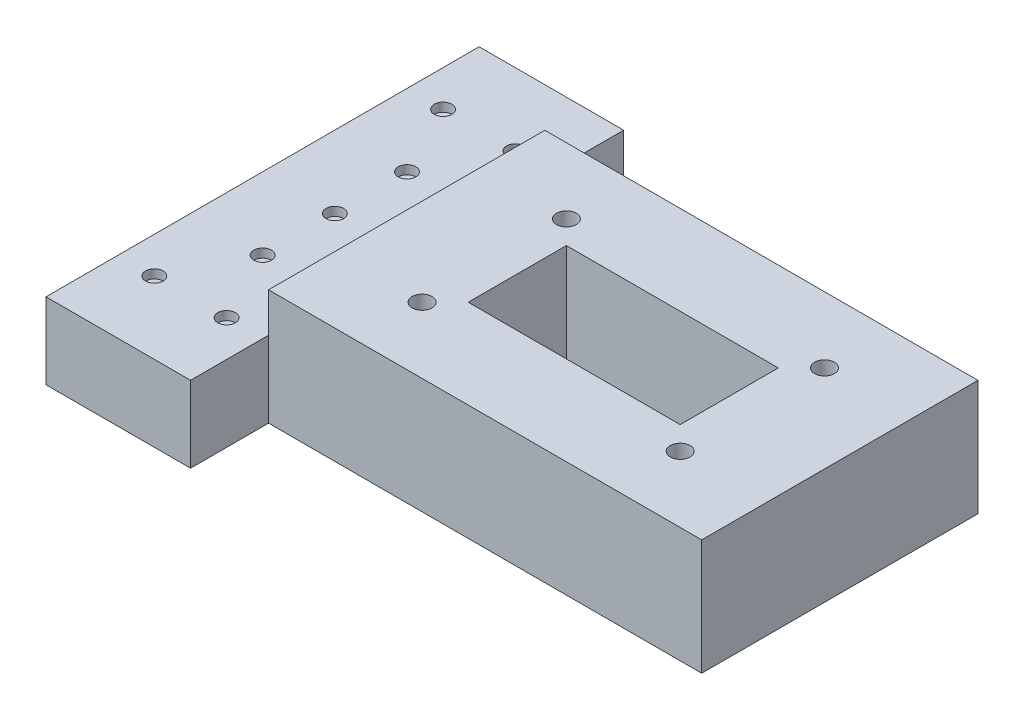
SolidWorks part; units mm, degrees
ref_plane "Front Plane" through (0, 0, 0) normal (0, 0, 1) x (1, 0, 0)
ref_plane "Top Plane" through (0, 0, 0) normal (0, 1, 0) x (1, 0, 0)
ref_plane "Right Plane" through (0, 0, 0) normal (1, 0, 0) x (0, 0, -1)
sketch "Sketch1" plane through (0, 0, 0) normal (0, 1, 0) x (1, 0, 0)
  line L0 (-111.76, 0) -> (-111.76, 9.42)
  line L1 (0, 0) -> (-111.76, 0)
  line L2 (0, 0) -> (0, 75.69)
  line L3 (0, 75.69) -> (-111.76, 75.69)
  line L4 (-111.76, 0) -> (-111.76, 9.42)
  line L5 (-111.76, 9.42) -> (-100.58, 9.42)
  line L7 (-111.76, 16.28) -> (-100.58, 16.28)
  line L8 (-111.76, 16.28) -> (-111.76, 75.69)
  line L9 (0, 0) -> (0, 37.845)
  line L10 (0, 37.845) -> (-111.76, 37.845)
  line L11 (-55.88, 75.69) -> (-55.88, 0)
  line L12 (-111.76, 66.27) -> (-100.58, 66.27)
  line L13 (-111.76, 59.41) -> (-100.58, 59.41)
  line L14 (0, 9.42) -> (-11.18, 9.42)
  line L15 (0, 16.28) -> (-11.18, 16.28)
  line L16 (0, 59.41) -> (-11.18, 59.41)
  line L17 (0, 66.27) -> (-11.18, 66.27)
  arc A0 (-100.58, 9.42) -> (-100.58, 16.28) centre (-100.58, 12.85) ccw
  arc A1 (-100.58, 66.27) -> (-100.58, 59.41) centre (-100.58, 62.84) cw
  arc A2 (-11.18, 9.42) -> (-11.18, 16.28) centre (-11.18, 12.85) cw
  arc A3 (-11.18, 66.27) -> (-11.18, 59.41) centre (-11.18, 62.84) ccw
  dimension "D1" = 111.76
  dimension "D2" = 75.69
sketch "Sketch2" plane through (0, 0, 0) normal (0, 1, 0) x (1, 0, 0)
  line L0 (-55.88, 0) -> (-55.88, 75.69)
  line L1 (-111.76, 0) -> (-121.76, 0)
  line L2 (-111.76, 0) -> (-111.76, -10)
  line L3 (-111.76, -10) -> (-121.76, -10)
  line L4 (-121.76, 0) -> (-121.76, -10)
  line L5 (0, 75.69) -> (10, 75.69)
  line L6 (0, 75.69) -> (0, 85.69)
  line L7 (0, 85.69) -> (10, 85.69)
  line L8 (10, 75.69) -> (10, 85.69)
  line L9 (-111.76, 37.845) -> (0, 37.845)
  circle A0 centre (-100.58, 12.85) radius 3.43
  circle A1 centre (-100.58, 12.85) radius 8
  circle A2 centre (-100.58, 62.84) radius 8
  circle A3 centre (-11.18, 12.85) radius 8
  circle A4 centre (-11.18, 62.84) radius 8
  dimension "D1" = 10
  dimension "D2" = 10
  dimension "D3" = 10
  dimension "D4" = 10
sketch "Sketch3" plane through (0, 0, 0) normal (0, 1, 0) x (1, 0, 0)
  line L0 (-100.58, 54.84) -> (-92.58, 54.84)
  line L1 (-121.76, -10) -> (-108.58, -10)
  line L2 (-121.76, -10) -> (-121.76, 12.85)
  line L5 (-108.58, -10) -> (-11.18, -10)
  line L9 (10, 85.69) -> (-3.18, 85.69)
  line L10 (10, 85.69) -> (10, 62.84)
  line L14 (10, 62.84) -> (10, -10)
  line L15 (10, -10) -> (-3.18, -10)
  line L19 (-11.18, -10) -> (-3.18, -10)
  line L22 (-121.76, 12.85) -> (-121.76, 62.84)
  line L26 (-121.76, 62.84) -> (-121.76, 85.69)
  line L27 (-121.76, 85.69) -> (-108.58, 85.69)
  line L29 (-108.58, 85.69) -> (-11.18, 85.69)
  line L35 (-11.18, 85.69) -> (-3.18, 85.69)
  line L37 (-92.58, 62.84) -> (-92.58, 54.84)
  line L38 (-19.18, 12.85) -> (-19.18, 20.85)
  line L39 (-11.18, 20.85) -> (-19.18, 20.85)
  line L41 (-92.58, 54.84) -> (-19.18, 54.84)
  line L42 (-92.58, 54.84) -> (-92.58, 20.85)
  line L43 (-92.58, 20.85) -> (-19.18, 20.85)
  line L44 (-19.18, 54.84) -> (-19.18, 20.85)
  circle A1 centre (-11.18, 12.85) radius 8 construction
  circle A3 centre (-100.58, 62.84) radius 8 construction
  circle A8 centre (-100.58, 62.84) radius 3.43
  circle A9 centre (-11.18, 62.84) radius 3.43
  circle A10 centre (-11.18, 12.85) radius 3.43
  circle A11 centre (-100.58, 12.85) radius 3.43
sketch "Sketch4" plane through (0, 0, 0) normal (0, 1, 0) x (1, 0, 0)
  line L0 (-108.58, 62.84) -> (-108.58, 70.84)
  line L1 (-108.58, 12.85) -> (-108.58, 4.85)
  line L2 (-108.58, 70.84) -> (-121.76, 70.84)
  line L3 (-108.58, 70.84) -> (-108.58, 85.69)
  line L4 (-108.58, 85.69) -> (-121.76, 85.69)
  line L5 (-121.76, 70.84) -> (-121.76, 85.69)
  line L6 (-55.88, 0) -> (-55.88, 75.69)
  line L7 (-108.58, 4.85) -> (-121.76, 4.85)
  line L8 (-108.58, 4.85) -> (-108.58, -10)
  line L9 (-108.58, -10) -> (-121.76, -10)
  line L10 (-121.76, 4.85) -> (-121.76, -10)
  line L11 (0, 0) -> (-111.76, 0) construction
  line L12 (10, 4.85) -> (10, -10)
  line L13 (-3.18, -10) -> (10, -10)
  line L14 (-3.18, 4.85) -> (-3.18, -10)
  line L15 (-3.18, 4.85) -> (10, 4.85)
  line L16 (-3.18, 70.84) -> (10, 70.84)
  line L17 (10, 70.84) -> (10, 85.69)
  line L18 (-3.18, 85.69) -> (10, 85.69)
  line L19 (-3.18, 70.84) -> (-3.18, 85.69)
  circle A0 centre (-100.58, 62.84) radius 8 construction
  circle A1 centre (-100.58, 12.85) radius 8 construction
sketch "Sketch8" plane through (0, 0, 0) normal (0, 1, 0) x (1, 0, 0)
  line L1 (-92.58, 20.85) -> (-19.18, 20.85)
  line L2 (-92.58, 20.85) -> (-92.58, 54.84)
  line L3 (-92.58, 54.84) -> (-19.18, 54.84)
  line L4 (-19.18, 20.85) -> (-19.18, 54.84)
  line L5 (-121.76, 85.69) -> (10, 85.69)
  line L6 (-121.76, 85.69) -> (-121.76, -10)
  line L7 (-121.76, -10) -> (10, -10)
  line L8 (10, 85.69) -> (10, -10)
  circle A0 centre (-100.58, 12.85) radius 3.43
  circle A1 centre (-100.58, 62.84) radius 3.43
  circle A2 centre (-11.18, 62.84) radius 3.43
  circle A3 centre (-11.18, 12.85) radius 3.43
extrude "Boss-Extrude4" add sketch "Sketch8" along normal blind 40
sketch "Sketch9" plane through (0, 0, 0) normal (0, -1, 0) x (1, 0, 0)
  circle A0 centre (-100.58, -12.85) radius 8
  circle A1 centre (-11.18, -12.85) radius 8
  circle A2 centre (-11.18, -62.84) radius 8
  circle A3 centre (-100.58, -62.84) radius 8
extrude "Cut-Extrude2" cut sketch "Sketch9" against normal blind 8
sketch "Sketch10" plane through (0, 0, 0) normal (0, -1, 0) x (1, 0, 0)
  line L1 (-121.76, 10) -> (10, 10)
  line L2 (-121.76, 10) -> (-121.76, 60)
  line L3 (-121.76, 60) -> (10, 60)
  line L4 (10, 10) -> (10, 60)
  line L5 (-121.76, 60) -> (-108.58, 60)
  line L6 (-121.76, 60) -> (-121.76, 45.15)
  line L7 (-121.76, 45.15) -> (-108.58, 45.15)
  line L8 (-108.58, 60) -> (-108.58, 45.15)
  dimension "D1" = 50
  dimension "D2" = 13.18
  dimension "D3" = 14.85
sketch "Sketch11" plane through (0, 40, 0) normal (0, 1, 0) x (1, 0, 0)
  line L1 (-121.76, -60) -> (10, -60)
  line L2 (-121.76, -60) -> (-121.76, -10)
  line L3 (-121.76, -10) -> (10, -10)
  line L4 (10, -60) -> (10, -10)
sketch "Sketch12" plane through (0, 0, 0) normal (0, -1, 0) x (1, 0, 0)
  line L1 (-121.76, 10) -> (-130.88, 10)
  line L2 (-130.88, 10) -> (19.12, 10)
  line L3 (19.12, 10) -> (19.12, -85.69)
  line L4 (19.12, -85.69) -> (-130.88, -85.69)
  line L5 (-130.88, -85.69) -> (-130.88, 10)
  line M9 (-121.76, 10) -> (-121.76, -85.69)
  line M11 (10, -85.69) -> (10, 10)
extrude "Boss-Extrude5" add sketch "Sketch12" against normal up to surface (40 mm away) contours L5 L4 L1 M9 | L4 L3 L2 M11 up to face at (-11.18, 40, -59.41)
sketch "Sketch13" plane through (0, 0, 0) normal (0, -1, 0) x (1, 0, 0)
  line L0 (-130.88, 10) -> (-130.88, -85.69)
  line L5 (-130.88, 10) -> (-130.88, 37.02)
  line L7 (-130.88, 37.02) -> (-180.93, 37.02)
  line L8 (-130.88, 37.02) -> (-130.88, -112.98)
  line L9 (-130.88, -112.98) -> (-180.93, -112.98)
  line L10 (-180.93, 37.02) -> (-180.93, -112.98)
  line M10 (-130.88, 10) -> (-130.88, -85.69)
  dimension "D2" = 95.69
  dimension "D3" = 50.05
  dimension "D4" = 150
extrude "Boss-Extrude6" add sketch "Sketch13" against normal blind 26.38 contours L7 L10 L9 L8 L5 M10
sketch "Sketch14" plane through (0, 26.38, 0) normal (0, 1, 0) x (1, 0, 0)
  line L0 (-130.88, -60.05) -> (-105.88, -60.05)
  line L1 (-130.88, -60.05) -> (19.12, -60.05)
  line L2 (-130.88, -60.05) -> (-130.88, -10)
  line L3 (-130.88, -10) -> (19.12, -10)
  line L4 (19.12, -60.05) -> (19.12, -10)
  line L5 (-105.88, -60.05) -> (-80.88, -60.05)
  line L6 (-80.88, -60.05) -> (-55.88, -60.05)
  line L7 (-55.88, -60.05) -> (-30.88, -60.05)
  line L8 (-30.88, -60.05) -> (-5.88, -60.05)
  line L9 (-5.88, -60.05) -> (19.12, -60.05)
  line L10 (19.12, -35.025) -> (-130.88, -35.025)
  line L11 (-5.88, -60.05) -> (-5.88, -35.025)
  line L12 (-30.88, -60.05) -> (-30.88, -35.025)
  line L13 (-55.88, -60.05) -> (-55.88, -35.025)
  line L14 (-5.88, -35.025) -> (-5.88, -10)
  line L15 (-30.88, -35.025) -> (-30.88, -10)
  line L16 (-55.88, -35.025) -> (-55.88, -10)
  circle A0 centre (-30.88, -35.025) radius 3.05
  circle A3 centre (-5.88, -47.5375) radius 3.05
  circle A4 centre (-5.88, -22.5125) radius 3.05
  circle A5 centre (-55.88, -22.5125) radius 3.05
  circle A6 centre (-55.88, -47.5375) radius 3.05
  circle A7 centre (-105.88, -22.5125) radius 3.05
  circle A8 centre (-105.88, -47.5375) radius 3.05
  circle A9 centre (-80.88, -35.025) radius 3.05
sketch "Sketch15" plane through (0, 26.38, 0) normal (0, 1, 0) x (1, 0, 0)
  line L0 (-155.905, -37.02) -> (-155.905, 112.98)
  line L1 (-130.88, -37.02) -> (-180.93, -37.02) construction
  line L2 (-130.88, 112.98) -> (-180.93, 112.98) construction
  line L3 (-180.93, 112.98) -> (-180.93, -37.02)
  line L4 (-180.93, 37.98) -> (-180.93, 62.98)
  line L5 (-180.93, 62.98) -> (-180.93, 87.98)
  line L6 (-180.93, 37.98) -> (-180.93, 15.358)
  line L7 (-180.93, -37.02) -> (-180.93, -12.02)
  line L8 (-180.93, -12.02) -> (-155.905, -12.02)
  line L9 (-155.905, -12.02) -> (-130.88, -12.02)
  line L10 (-130.88, -37.02) -> (-130.88, -10) construction
  line L11 (-155.905, -12.02) -> (-155.905, 12.98)
  line L12 (-155.905, 37.98) -> (-180.93, 37.98)
  line L13 (-155.905, 12.98) -> (-180.93, 12.98)
  line L14 (-180.93, 62.98) -> (-155.905, 62.98)
  line L15 (-180.93, 87.98) -> (-155.905, 87.98)
  line L16 (-155.905, 87.98) -> (-130.88, 87.98)
  line L17 (-130.88, 85.69) -> (-130.88, 112.98) construction
  circle A0 centre (-168.4175, 87.98) radius 3.05
  circle A1 centre (-143.3925, 87.98) radius 3.05
  circle A2 centre (-155.905, 62.98) radius 3.05
  circle A3 centre (-155.905, 37.98) radius 3.05
  circle A4 centre (-155.905, 12.98) radius 3.05
  circle A5 centre (-168.4175, -12.02) radius 3.05
  circle A6 centre (-143.3925, -12.02) radius 3.05
extrude "Cut-Extrude4" cut sketch "Sketch15" against normal blind 3.05 contours A0 | A1 | A2 | A3 | A4 | A6 | A5
extrude "Cut-Extrude3" cut sketch "Sketch14" against normal blind 3.05 contours A7 | A8 | A9 L10 | A9 L10 | L16 A5 | L16 A5 | L13 A6 | L13 A6 | L10 A0 L12 | L12 A0 L10 | L10 A0 L15 | L15 A0 L10 | L14 A4 | L14 A4 | L11 A3 | L11 A3
